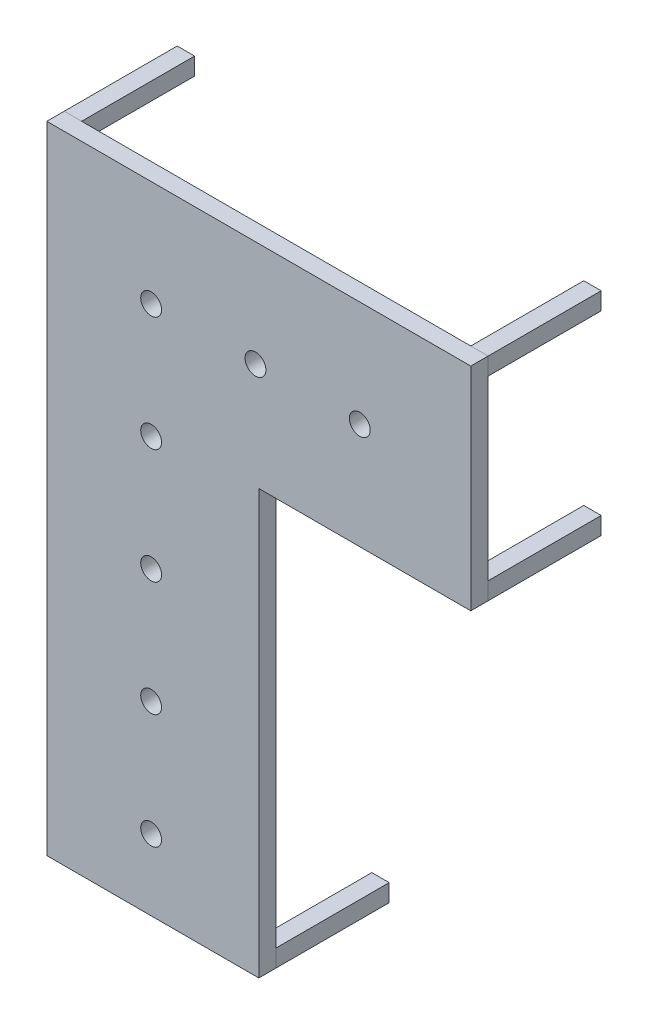
SolidWorks part; units mm, degrees
ref_plane "Front Plane" through (0, 0, 0) normal (0, 0, 1) x (1, 0, 0)
ref_plane "Top Plane" through (0, 0, 0) normal (0, 1, 0) x (1, 0, 0)
ref_plane "Right Plane" through (0, 0, 0) normal (1, 0, 0) x (0, 0, -1)
sketch "Sketch3" plane through (0, 0, 0) normal (0, 0, 1) x (1, 0, 0)
  line L0 (2438.4, -1219.2) -> (2438.4, 0)
  line L1 (0, 0) -> (2438.4, 0)
  line L2 (2438.4, -1219.2) -> (1219.2, -1219.2)
  line L3 (1219.2, -3657.6) -> (0, -3657.6)
  line L4 (0, 0) -> (0, -3657.6)
  line L5 (1219.2, -1219.2) -> (1219.2, -3657.6)
  dimension "D1" = 2438.4
  dimension "D2" = 1219.2
  dimension "D3" = 1219.2
  dimension "D4" = 2438.4
extrude "Boss-Extrude1" add sketch "Sketch3" along normal blind 100
sketch "Sketch4" plane through (0, 0, 0) normal (0, 0, -1) x (-1, 0, 0)
  line L0 (-2338.4, -100) -> (-2438.4, -100)
  line L1 (0, -3657.6) -> (-100, -3657.6)
  line L2 (0, -3657.6) -> (0, -3557.6)
  line L3 (0, -3557.6) -> (-100, -3557.6)
  line L4 (-100, -3657.6) -> (-100, -3557.6)
  line L5 (-2338.4, -100) -> (-2338.4, 0)
  line L6 (-2338.4, 0) -> (-2438.4, 0)
  line L7 (-2438.4, -100) -> (-2438.4, 0)
  line L8 (0, -100) -> (-100, -100)
  line L9 (0, -100) -> (0, 0)
  line L10 (0, 0) -> (-100, 0)
  line L11 (-100, -100) -> (-100, 0)
  line L13 (-1119.2, -3657.6) -> (-1219.2, -3657.6)
  line L14 (-1119.2, -3657.6) -> (-1119.2, -3557.6)
  line L15 (-1119.2, -3557.6) -> (-1219.2, -3557.6)
  line L16 (-1219.2, -3657.6) -> (-1219.2, -3557.6)
  line L17 (-1119.2, -1219.2) -> (-1219.2, -1219.2)
  line L18 (-1119.2, -1219.2) -> (-1119.2, -1119.2)
  line L19 (-1119.2, -1119.2) -> (-1219.2, -1119.2)
  line L20 (-1219.2, -1219.2) -> (-1219.2, -1119.2)
  line L21 (-2338.4, -1219.2) -> (-2438.4, -1219.2)
  line L22 (-2338.4, -1219.2) -> (-2338.4, -1119.2)
  line L23 (-2338.4, -1119.2) -> (-2438.4, -1119.2)
  line L24 (-2438.4, -1219.2) -> (-2438.4, -1119.2)
  line L25 (0, -1219.2) -> (-100, -1219.2)
  line L26 (0, -1219.2) -> (0, -1119.2)
  line L27 (0, -1119.2) -> (-100, -1119.2)
  line L28 (-100, -1219.2) -> (-100, -1119.2)
  line L29 (0, 0) -> (0, -3657.6) construction
  dimension "D1" = 100
  dimension "D2" = 100
  dimension "D3" = 100
  dimension "D4" = 100
  dimension "D5" = 100
  dimension "D6" = 100
  dimension "D7" = 100
  dimension "D8" = 100
  dimension "D9" = 100
  dimension "D10" = 100
  dimension "D11" = 100
  dimension "D12" = 100
  dimension "D13" = 100
  dimension "D14" = 100
extrude "Boss-Extrude2" add sketch "Sketch4" along normal blind 650 separate body
sketch "Sketch5" plane through (0, 0, 0) normal (0, 0, -1) x (-1, 0, 0)
  line L3 (0, 0) -> (0, -3657.6) construction
  line L4 (-1219.2, -1219.2) -> (-2438.4, -1219.2) construction
  circle A0 centre (-600, -3249.2) radius 60
  circle A1 centre (-600, -2589.2) radius 60
  circle A2 centre (-600, -1929.2) radius 60
  circle A3 centre (-600, -1269.2) radius 60
  circle A4 centre (-600, -609.2) radius 60
  circle A8 centre (-1200, -609.2) radius 60
  circle A12 centre (-1800, -609.2) radius 60
  circle A28 centre (-1200, -2589.2) radius 60 [skipped]
  circle A29 centre (-1200, -1929.2) radius 60 [skipped]
  circle A30 centre (-1200, -1269.2) radius 60 [skipped]
  circle A31 centre (-1800, -2589.2) radius 60 [skipped]
  circle A32 centre (-1800, -1929.2) radius 60 [skipped]
  circle A33 centre (-1800, -1269.2) radius 60 [skipped]
  circle A34 centre (-2400, -2589.2) radius 60 [skipped]
  circle A35 centre (-2400, -1929.2) radius 60 [skipped]
  circle A36 centre (-2400, -1269.2) radius 60 [skipped]
  circle A37 centre (-1200, -3249.2) radius 60 [skipped]
  circle A38 centre (-1800, -3249.2) radius 60 [skipped]
  circle A39 centre (-2400, -3249.2) radius 60 [skipped]
  circle A40 centre (-2400, -609.2) radius 60 [skipped]
  dimension "D1" = 5
  dimension "D4" = 600
  dimension "D3" = 610
  dimension "D2" = 4
extrude "Cut-Extrude2" cut sketch "Sketch5" against normal through all
equation "\"VV\"=100"
equation "\"D2@Sketch4\"=\"VV\""
equation "\"D1@Sketch4\"=\"VV\""
